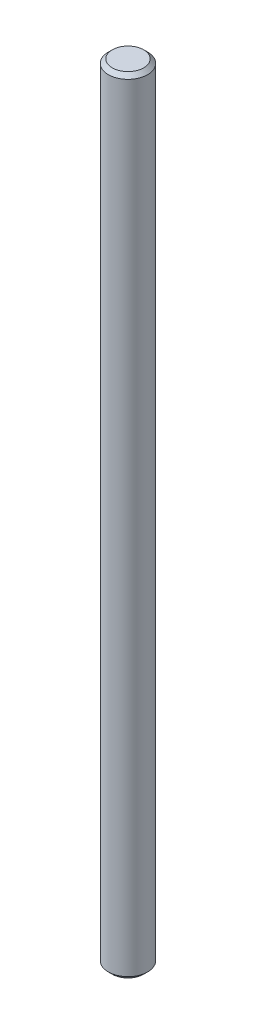
SolidWorks part; units mm, degrees
material "Alliage 1060"
ref_plane "Plan de face" through (0, 0, 0) normal (0, 0, 1) x (1, 0, 0)
ref_plane "Plan de dessus" through (0, 0, 0) normal (0, 1, 0) x (1, 0, 0)
ref_plane "Plan de droite" through (0, 0, 0) normal (1, 0, 0) x (0, 0, -1)
sketch "Esquisse1" plane through (0, 0, 0) normal (0, 1, 0) x (1, 0, 0)
  circle A0 centre (0, 0) radius 5
  dimension "D1" = 10
extrude "Boss.-Extru.1" add sketch "Esquisse1" along normal blind 200
chamfer "Chanfrein1" distance 1 angle 45 2 edges at (0, 0, 5) (0, 200, 5)
